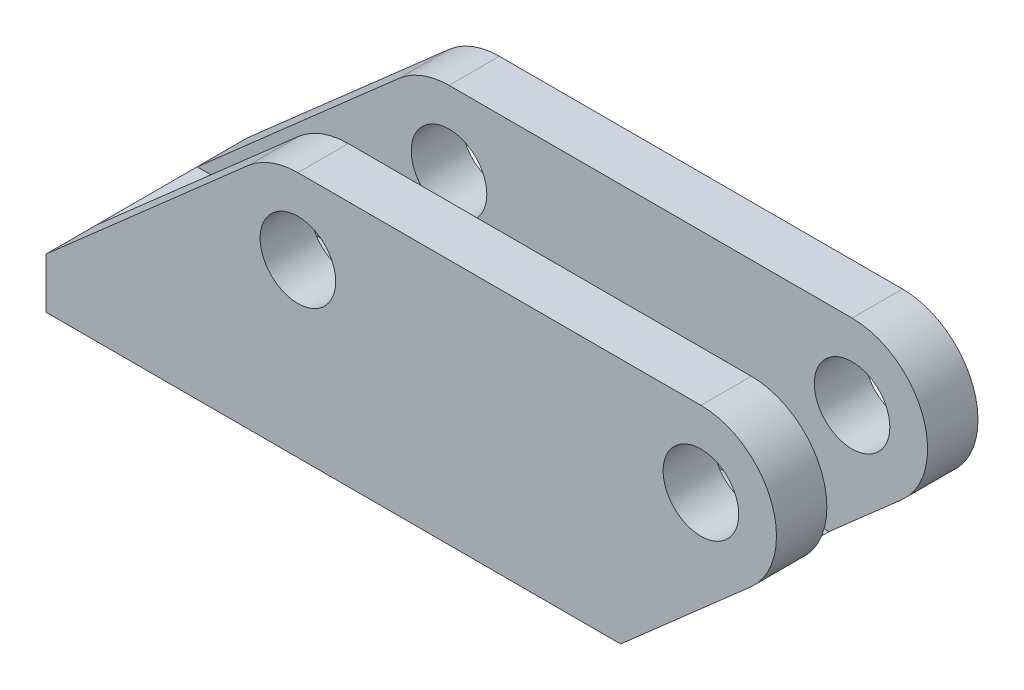
SolidWorks part; units mm, degrees
ref_plane "Front Plane" through (0, 0, 0) normal (0, 0, 1) x (1, 0, 0)
ref_plane "Top Plane" through (0, 0, 0) normal (0, 1, 0) x (1, 0, 0)
ref_plane "Right Plane" through (0, 0, 0) normal (1, 0, 0) x (0, 0, -1)
sketch "Sketch1" plane through (0, 0, 0) normal (0, 0, 1) x (1, 0, 0)
  line L5 (-6.2906, 13.5022) -> (-31.75, -8.89)
  line L6 (0, 6.35) -> (50.8, 6.35) construction
  line L14 (-31.75, -15.24) -> (-31.75, -8.89)
  line L15 (0, 6.35) -> (0, -15.24) construction
  line L16 (0, 15.875) -> (50.8, 15.875)
  line L17 (57.0906, -0.8022) -> (40.6752, -15.24)
  line L18 (-31.75, -15.24) -> (40.6752, -15.24)
  circle A0 centre (0, 6.35) radius 4.7625
  circle A1 centre (0, 6.35) radius 9.525
  circle A2 centre (50.8, 6.35) radius 4.7625
  circle A3 centre (50.8, 6.35) radius 9.525
  point P0 (0, 0)
  point P6 (31.75, -12.7)
  point P7 (31.75, -2.6516)
  point P8 (0, 6.35)
extrude "Boss-Extrude1" add sketch "Sketch1" along normal blind 25.4
sketch "Sketch2" plane through (0, -15.24, 0) normal (0, -1, 0) x (-1, 0, 0)
  line L0 (0, -12.7) -> (0, 0)
  line L2 (19.05, -12.7) -> (-19.05, -12.7) construction
  circle A0 centre (-19.05, -12.7) radius 3.175
  circle A1 centre (19.05, -12.7) radius 3.175
  point P7 (0, -12.7)
extrude "Cut-Extrude1" cut sketch "Sketch2" against normal through all
sketch "Sketch3" plane through (-31.75, 0, 0) normal (-1, 0, 0) x (0, 0, 1)
  line L0 (0, -8.89) -> (6.35, -8.89)
  line L1 (25.4, -8.89) -> (0, -8.89) construction
  line L3 (6.35, -8.89) -> (19.05, -8.89)
  line L4 (6.35, -8.89) -> (6.35, 19.9155)
  line L5 (6.35, 19.9155) -> (19.05, 19.9155)
  line L6 (19.05, -8.89) -> (19.05, 19.9155)
  line M9 (25.4, -8.89) -> (0, -8.89)
extrude "Cut-Extrude2" cut sketch "Sketch3" against normal through all contours L6 L5 L4 M9
